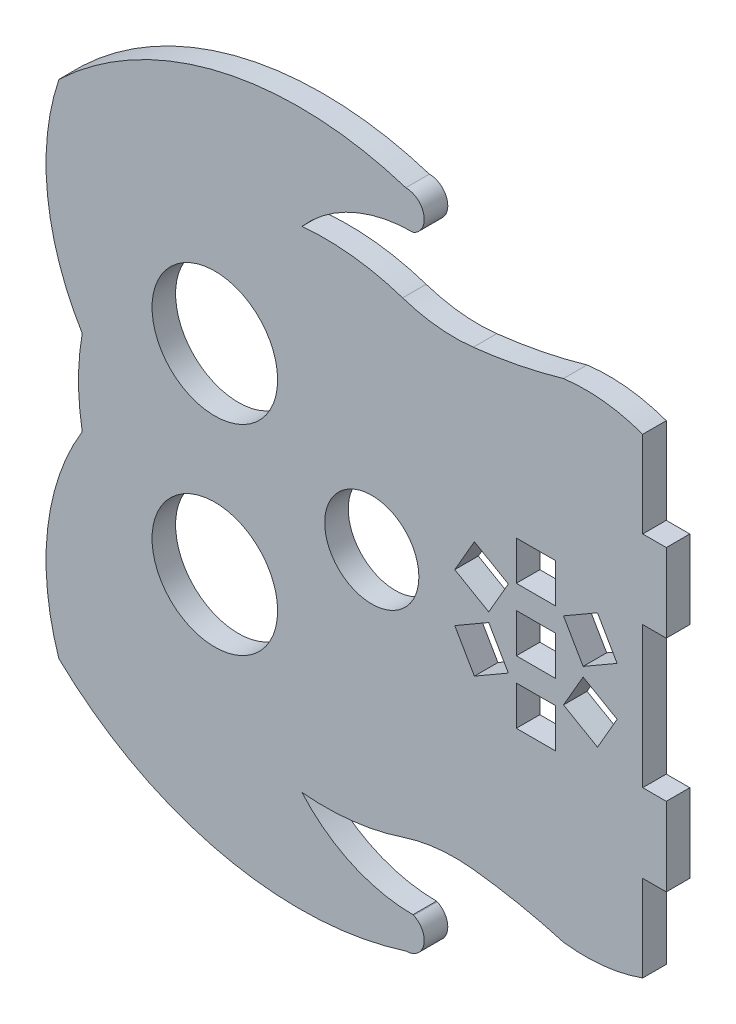
SolidWorks part; units mm, degrees
ref_plane "Front Plane" through (0, 0, 0) normal (0, 0, 1) x (1, 0, 0)
ref_plane "Top Plane" through (0, 0, 0) normal (0, 1, 0) x (1, 0, 0)
ref_plane "Right Plane" through (0, 0, 0) normal (1, 0, 0) x (0, 0, -1)
sketch "Sketch2" plane through (0, 0, 0) normal (0, 0, 1) x (1, 0, 0)
  line L0 (81.0321, 50.1813) -> (81.0321, 60.1813)
  line L1 (81.0321, 60.1813) -> (78.0321, 60.1813)
  line L2 (78.0321, 60.1813) -> (78.0321, 71.1813)
  line L15 (78.0321, 11.1813) -> (78.0321, 22.1813)
  line L16 (78.0321, 22.1813) -> (81.0321, 22.1813)
  line L17 (81.0321, 22.1813) -> (81.0321, 32.1813)
  line L18 (81.0321, 32.1813) -> (78.0321, 32.1813)
  line L19 (78.0321, 32.1813) -> (78.0321, 50.1813)
  line L20 (78.0321, 50.1813) -> (81.0321, 50.1813)
  line L21 (61.923, 43.6813) -> (61.923, 38.6813)
  line L22 (61.923, 38.6813) -> (66.923, 38.6813)
  line L23 (66.923, 38.6813) -> (66.923, 43.6813)
  line L24 (66.923, 43.6813) -> (61.923, 43.6813)
  line L25 (61.923, 35.6813) -> (61.923, 30.6813)
  line L26 (61.923, 30.6813) -> (66.923, 30.6813)
  line L27 (66.923, 30.6813) -> (66.923, 35.6813)
  line L28 (66.923, 35.6813) -> (61.923, 35.6813)
  line L29 (72.2663, 48.5964) -> (67.9362, 46.0964)
  line L30 (67.9362, 46.0964) -> (70.4362, 41.7662)
  line L31 (70.4362, 41.7662) -> (74.7663, 44.2662)
  line L32 (74.7663, 44.2662) -> (72.2663, 48.5964)
  line L33 (67.9362, 36.2662) -> (72.2663, 33.7662)
  line L34 (72.2663, 33.7662) -> (74.7663, 38.0964)
  line L35 (74.7663, 38.0964) -> (70.4362, 40.5964)
  line L36 (70.4362, 40.5964) -> (67.9362, 36.2662)
  line L37 (61.923, 51.6813) -> (61.923, 46.6813)
  line L38 (61.923, 46.6813) -> (66.923, 46.6813)
  line L39 (66.923, 46.6813) -> (66.923, 51.6813)
  line L40 (66.923, 51.6813) -> (61.923, 51.6813)
  line L41 (56.5798, 33.7662) -> (60.9099, 36.2662)
  line L42 (60.9099, 36.2662) -> (58.4099, 40.5964)
  line L43 (58.4099, 40.5964) -> (54.0798, 38.0964)
  line L44 (54.0798, 38.0964) -> (56.5798, 33.7662)
  line L45 (60.9099, 46.0964) -> (56.5798, 48.5964)
  line L46 (56.5798, 48.5964) -> (54.0798, 44.2662)
  line L47 (54.0798, 44.2662) -> (58.4099, 41.7662)
  line L48 (58.4099, 41.7662) -> (60.9099, 46.0964)
  line L49 (78.0321, 41.1813) -> (23.507, 41.1813) construction
  circle A0 centre (23.507, 53.9313) radius 8
  circle A1 centre (43.507, 41.1813) radius 6
  circle A2 centre (23.507, 28.4313) radius 8
  arc A12 (47.4371, 70.9365) -> (34.6136, 72.416) centre (37.507, 41.1813) ccw
  arc A13 (6.6103, 46.6008) -> (3.6415, 73.1505) centre (33.7401, 63.0753) cw
  arc A14 (3.6415, 73.1505) -> (47.8479, 83.2972) centre (34.2837, 41.0216) cw
  arc A15 (47.8479, 83.2972) -> (48.857, 78.8669) centre (47.8663, 80.9713) cw
  arc A16 (48.857, 78.8669) -> (48.7553, 78.8353) centre (56.7811, 53.1787) ccw
  arc A17 (48.7553, 78.8353) -> (34.6136, 72.416) centre (48.758, 60.0425) ccw
  arc A18 (56.4384, 69.9888) -> (67.9362, 72.2842) centre (48.6767, 138.8111) ccw
  arc A19 (67.9362, 72.2842) -> (78.0321, 71.1813) centre (70.7118, 50.9322) cw
  arc A20 (6.6103, 35.7618) -> (3.6415, 9.2121) centre (33.7401, 19.2873) ccw
  arc A21 (3.6415, 9.2121) -> (47.8479, -0.9345) centre (34.2837, 41.341) ccw
  arc A22 (47.8479, -0.9345) -> (48.857, 3.4957) centre (47.8663, 1.3913) ccw
  arc A23 (48.857, 3.4957) -> (48.7553, 3.5274) centre (56.7811, 29.1839) cw
  arc A24 (48.7553, 3.5274) -> (34.6136, 9.9466) centre (48.758, 22.3201) cw
  arc A25 (67.9362, 10.0784) -> (78.0321, 11.1813) centre (70.7118, 31.4304) ccw
  arc A26 (56.4384, 12.3738) -> (67.9362, 10.0784) centre (48.6767, -56.4485) cw
  arc A27 (56.4384, 69.9888) -> (47.4371, 70.9365) centre (54.085, 90.8565) cw
  arc A28 (56.4384, 12.3738) -> (47.4371, 11.4261) centre (54.085, -8.4939) ccw
  arc A29 (6.6103, 46.6008) -> (6.6103, 35.7618) centre (37.507, 41.1813) ccw
  arc A30 (34.6136, 9.9466) -> (47.4371, 11.4261) centre (37.507, 41.1813) ccw
  point P89 (50.8177, 69.5856)
  point P92 (50.8177, 12.777)
  dimension "D2" = 21
  dimension "D3" = 21
  dimension "D4" = 12.75
  dimension "D5" = 12.75
  dimension "D1" = 11
extrude "Boss-Extrude1" add sketch "Sketch2" along normal blind 3
